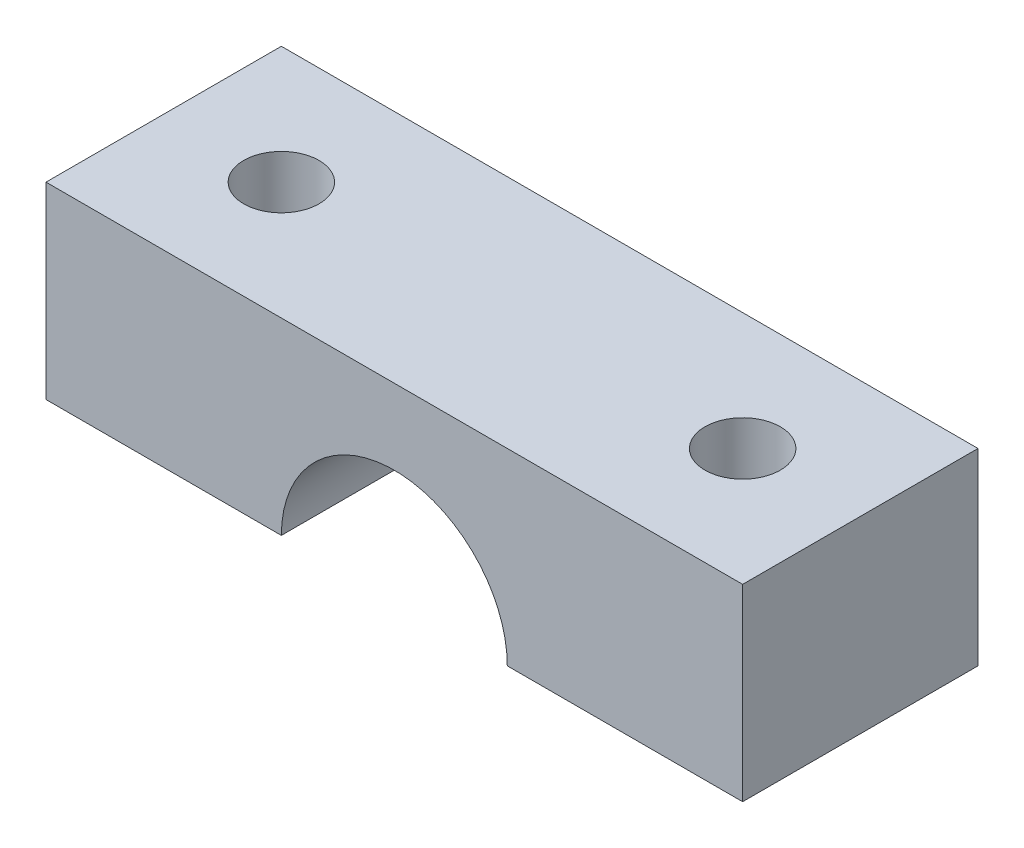
SolidWorks part; units mm, degrees
ref_plane "Front Plane" through (0, 0, 0) normal (0, 0, 1) x (1, 0, 0)
ref_plane "Top Plane" through (0, 0, 0) normal (0, 1, 0) x (1, 0, 0)
ref_plane "Right Plane" through (0, 0, 0) normal (1, 0, 0) x (0, 0, -1)
sketch "Sketch1" plane through (0, 0, 0) normal (0, 1, 0) x (1, 0, 0)
  line L1 (0, 0) -> (-29.6, 0)
  line L2 (0, 0) -> (0, 10)
  line L3 (0, 10) -> (-29.6, 10)
  line L4 (-29.6, 0) -> (-29.6, 10)
  dimension "D1" = 10
  dimension "D2" = 29.6
extrude "Boss-Extrude1" add sketch "Sketch1" along normal blind 8
sketch "Sketch2" plane through (0, 0, 0) normal (0, 0, 1) x (1, 0, 0)
  line L0 (-14.8, 8) -> (-14.8, 0) construction
  line L1 (-29.6, 8) -> (0, 8) construction
  line L2 (-29.6, 0) -> (0, 0) construction
  circle A0 centre (-14.8, 0) radius 4.8
extrude "Cut-Extrude1" cut sketch "Sketch2" against normal blind 10 contours A0
ref_plane "Plane1" through (-10, 0, -10) normal (-1, 0, 0) x (0, 0, 1)
sketch "Sketch4" plane through (0, 0, 0) normal (0, -1, 0) x (1, 0, 0)
  line L0 (0, 0) -> (-10, -10) construction
  line L1 (-10, -7.25) -> (-10, -12.75) construction
  line L2 (0, -10) -> (-10, -10) construction
  line L3 (-29.6, 0) -> (-19.6, -10) construction
  circle A0 centre (-24.6, -5) radius 1.6
  circle A1 centre (-5, -5) radius 1.6
extrude "Cut-Extrude2" cut sketch "Sketch4" against normal blind 8 contours A0
sketch "Sketch7" plane through (0, 0, 0) normal (0, -1, 0) x (1, 0, 0)
  line L0 (0, 0) -> (-10, -10) construction
  line L1 (-10, -7.25) -> (-10, -12.75) construction
  line L2 (0, -10) -> (-10, -10) construction
  circle A0 centre (-5, -5) radius 1.6
extrude "Cut-Extrude3" cut sketch "Sketch7" against normal blind 8
